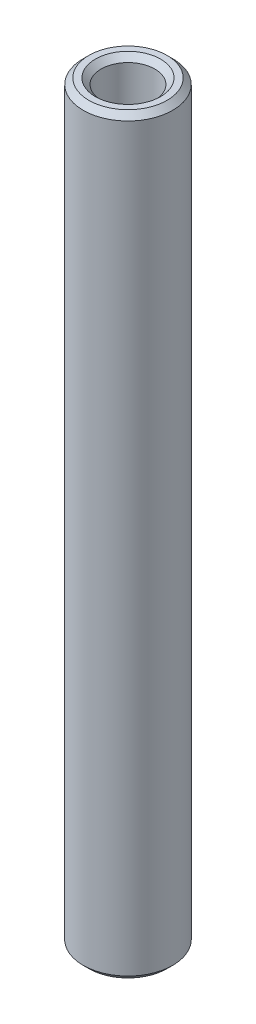
SolidWorks part; units mm, degrees
ref_plane "Front Plane" through (0, 0, 0) normal (0, 0, 1) x (1, 0, 0)
ref_plane "Top Plane" through (0, 0, 0) normal (0, 1, 0) x (1, 0, 0)
ref_plane "Right Plane" through (0, 0, 0) normal (1, 0, 0) x (0, 0, -1)
sketch "Sketch1" plane through (0, 0, 0) normal (0, 1, 0) x (1, 0, 0)
  circle A0 centre (0, 0) radius 1.9844
  circle A1 centre (0, 0) radius 1.1906
  dimension "D1" = 3.9688
  dimension "D2" = 0.7937
extrude "Boss-Extrude1" add sketch "Sketch1" along normal mid plane 33.3375
chamfer "Chamfer1" distance 0.254 angle 45 4 edges at (0, -16.6687, 1.1906) (0, -16.6687, 1.9844) (0, 16.6687, 1.1906) (0, 16.6687, 1.9844)
